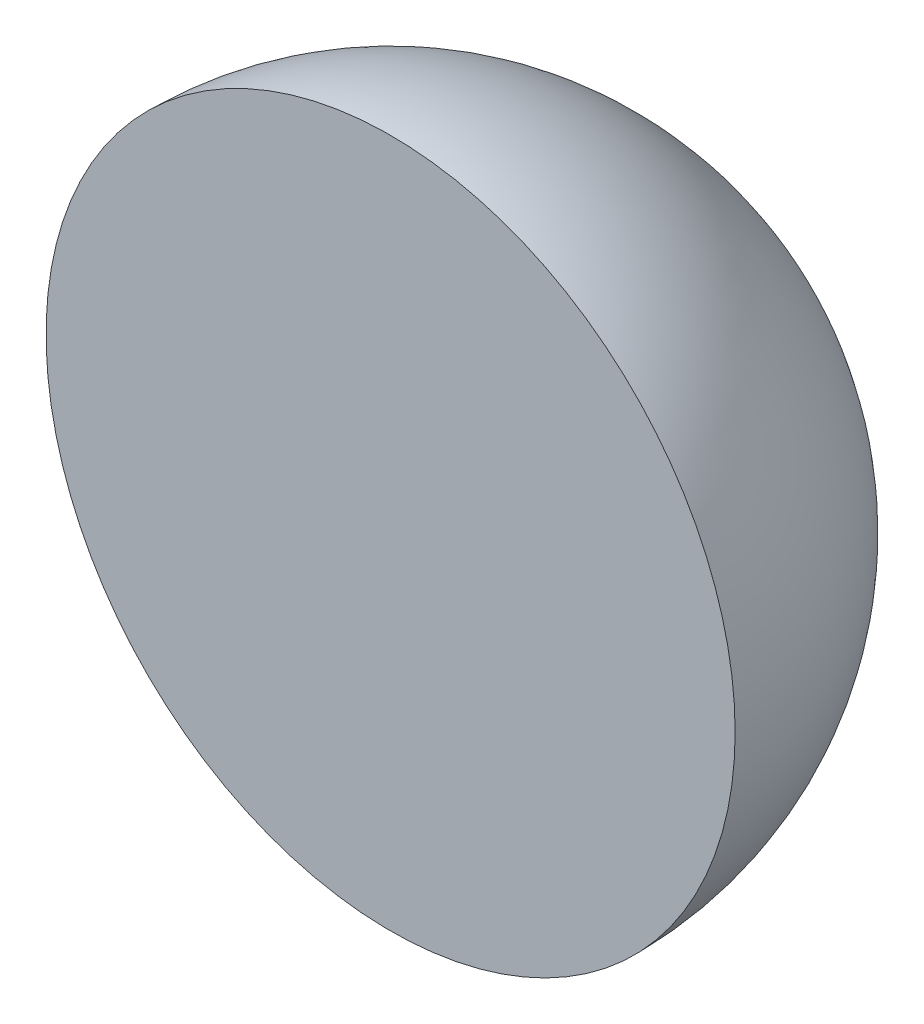
SolidWorks part; units mm, degrees
ref_plane "Płaszczyzna przednia" through (0, 0, 0) normal (0, 0, 1) x (1, 0, 0)
ref_plane "Płaszczyzna górna" through (0, 0, 0) normal (0, 1, 0) x (1, 0, 0)
ref_plane "Płaszczyzna prawa" through (0, 0, 0) normal (1, 0, 0) x (0, 0, -1)
sketch "Szkic1" plane through (0, 0, 0) normal (0, 0, 1) x (1, 0, 0)
  line L0 (0, 0) -> (0, 6190) construction
  line L1 (0, 0) -> (0, 6190)
  arc A0 (0, 6190) -> (0, 0) centre (0, 3095) cw
  dimension "D1" = 6190
revolve "Obrót1" add sketch "Szkic1" angle 180 about L0
